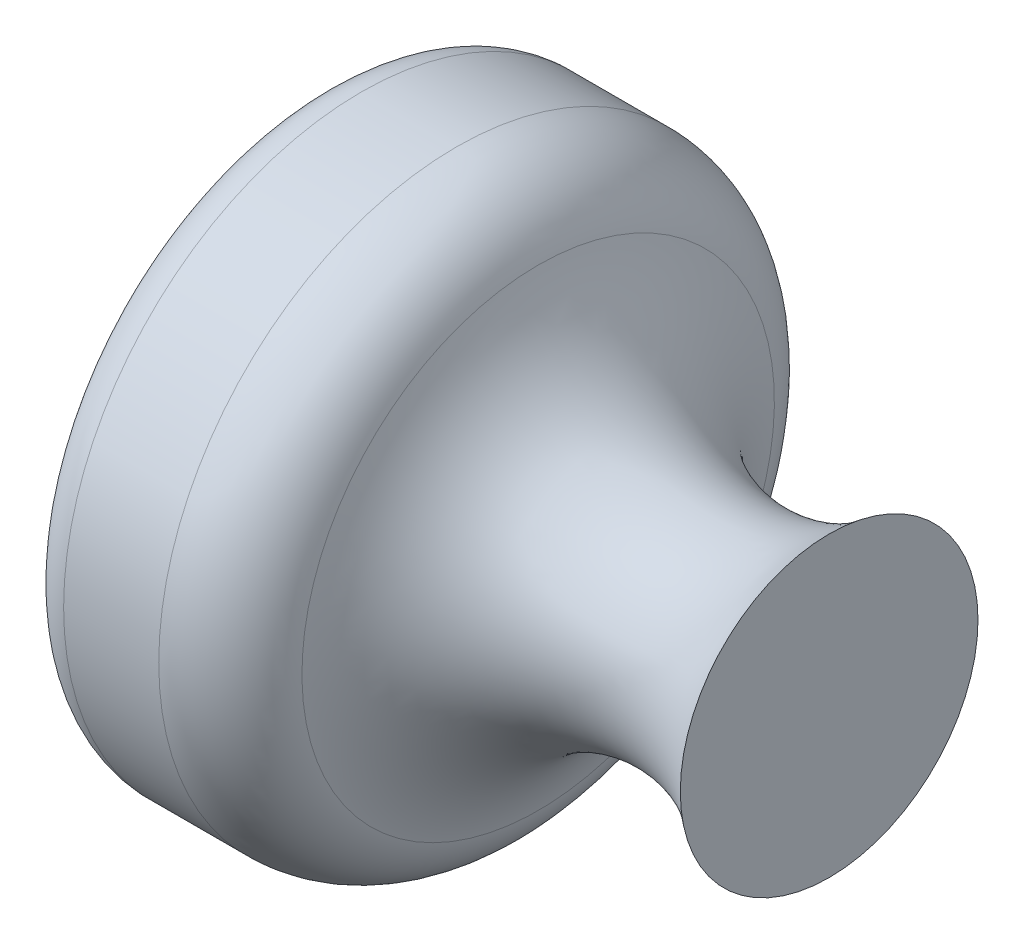
SolidWorks part; units mm, degrees
ref_plane "Front Plane" through (0, 0, 0) normal (0, 0, 1) x (1, 0, 0)
ref_plane "Top Plane" through (0, 0, 0) normal (0, 1, 0) x (1, 0, 0)
ref_plane "Right Plane" through (0, 0, 0) normal (1, 0, 0) x (0, 0, -1)
sketch "Sketch1" plane through (0, 0, 0) normal (0, 0, 1) x (1, 0, 0)
  line L0 (-12, 0) -> (-12, 6)
  line L1 (-11, 7) -> (-8.7632, 7)
  line L3 (0, 3.5) -> (0, 0)
  line L4 (0, 0) -> (-12, 0)
  arc A0 (0, 3.5) -> (-6.8417, 5.5546) centre (-2.7584, 6.7332) cw
  arc A1 (-12, 6) -> (-11, 7) centre (-11, 6) cw
  arc A2 (-8.7632, 7) -> (-6.8417, 5.5546) centre (-8.7632, 5) cw
  point P8 (-12, 7)
  point P11 (-7, 7)
  dimension "D5" = 1
  dimension "D6" = 2
  dimension "D7" = 4.25
  dimension "D1" = 3.5
  dimension "D2" = 7
  dimension "D3" = 12
  dimension "D4" = 5
  dimension "D8" = 0
revolve "Revolve1" add sketch "Sketch1" angle 360 about L4
